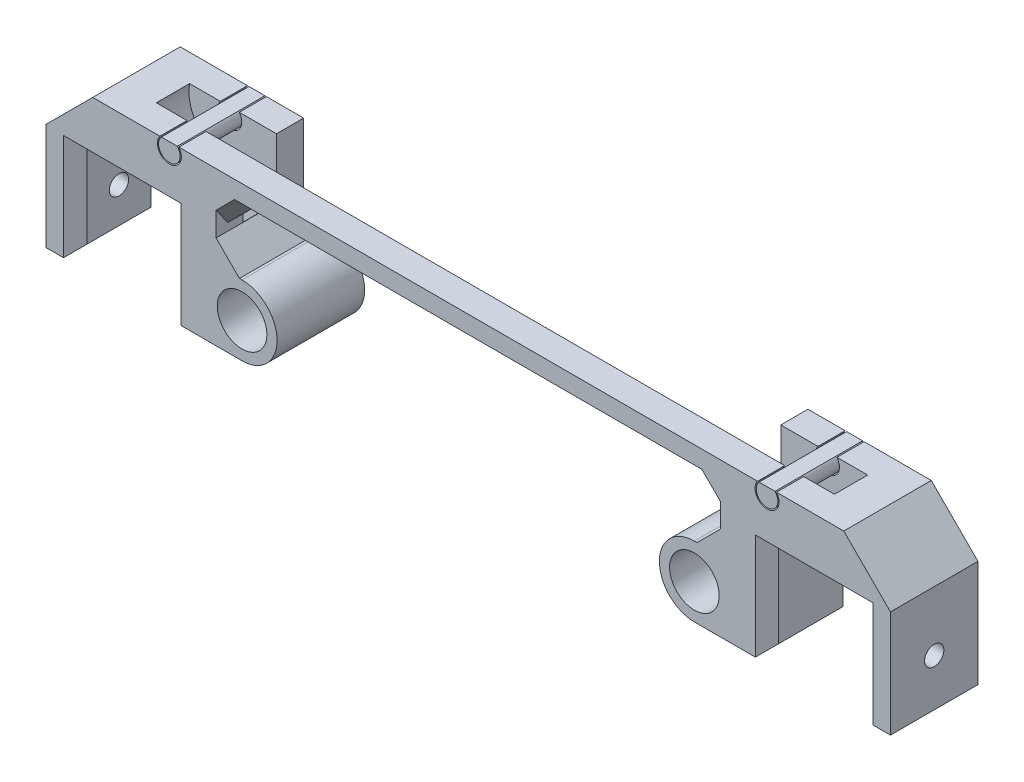
SolidWorks part; units mm, degrees
ref_plane "Front Plane" through (0, 0, 0) normal (0, 0, 1) x (1, 0, 0)
ref_plane "Top Plane" through (0, 0, 0) normal (0, 1, 0) x (1, 0, 0)
ref_plane "Right Plane" through (0, 0, 0) normal (1, 0, 0) x (0, 0, -1)
sketch "Sketch1" plane through (0, 0, 0) normal (0, 0, 1) x (1, 0, 0)
  line L0 (0, 0) -> (0, -36.7902) construction
  line L1 (-54.864, 0) -> (54.864, 0)
  line L2 (54.864, 0) -> (54.864, -27.0383)
  line L3 (54.864, -27.0383) -> (65.024, -27.0383)
  line L4 (65.024, -27.0383) -> (65.024, -6.5405)
  line L5 (65.024, -6.5405) -> (85.5218, -6.5405)
  line L6 (85.5218, -6.5405) -> (85.5218, -27.0383)
  line L7 (85.5218, -27.0383) -> (91.8718, -27.0383)
  line L8 (91.8718, -27.0383) -> (91.8718, 6.35)
  line L9 (91.8718, 6.35) -> (-91.8718, 6.35)
  line L10 (65.024, -6.5405) -> (65.024, -4.0005) construction
  line L11 (65.024, -4.0005) -> (65.024, 4.7625) construction
  line L12 (65.024, 4.7625) -> (65.024, 6.35) construction
  line L13 (65.024, 6.35) -> (65.024, 7.366) construction
  line L14 (-65.024, 6.35) -> (-65.024, 7.366) construction
  line L15 (-65.024, 4.7625) -> (-65.024, 6.35) construction
  line L16 (-65.024, -4.0005) -> (-65.024, 4.7625) construction
  line L17 (-65.024, -6.5405) -> (-65.024, -4.0005) construction
  line L18 (-91.8718, -27.0383) -> (-91.8718, 6.35)
  line L19 (-85.5218, -27.0383) -> (-91.8718, -27.0383)
  line L20 (-85.5218, -6.5405) -> (-85.5218, -27.0383)
  line L21 (-65.024, -6.5405) -> (-85.5218, -6.5405)
  line L22 (-65.024, -27.0383) -> (-65.024, -6.5405)
  line L23 (-54.864, -27.0383) -> (-65.024, -27.0383)
  line L24 (-54.864, 0) -> (-54.864, -27.0383)
  line L25 (65.024, -27.0383) -> (85.5218, -27.0383) construction
  circle A0 centre (65.024, 4.7625) radius 8.763 construction
  circle A1 centre (65.024, 4.7625) radius 2.6035
  circle A2 centre (-65.024, 4.7625) radius 8.763 construction
  circle A3 centre (-65.024, 4.7625) radius 2.6035
  point P26 (0, 6.35)
  dimension "D2" = 5.207
  dimension "D4" = 17.526
  dimension "D1" = 109.728
  dimension "D3" = 1.016
  dimension "D5" = 2.54
  dimension "D6" = 10.16
  dimension "D7" = 20.4978
  dimension "D8" = 6.35
  dimension "D9" = 6.35
  dimension "D10" = 130.048
  dimension "D11" = 171.0436
extrude "Boss-Extrude1" add sketch "Sketch1" along normal blind 19.05 contours L9 A3 L18 L19 L20 L21 L22 L23 L24 L1 L2 L3 L4 L5 L6 L7 L8 A1
hole_wizard "M5x0.8 Tapped Hole1" positions "Sketch9" profile "Sketch10" tap size "M5x0.8" standard "ANSI Metric" end condition up to next
sketch "Sketch9" plane through (91.8718, 0, 0) normal (1, 0, 0) x (0, 0, -1)
  line L0 (-9.525, -6.5405) -> (-9.525, -27.0383) construction
  line L1 (-19.05, -6.5405) -> (0, -6.5405) construction
  line L2 (-19.05, -27.0383) -> (0, -27.0383) construction
  point P0 (-9.525, -16.7894)
sketch "Sketch10" plane through (91.8718, -16.7894, 9.525) normal (0, 1, 0) x (0, 0, -1)
  line L0 (0, 0) -> (0, 6.35)
  line L1 (0, 6.35) -> (2.1, 6.35)
  line L2 (2.1, 6.35) -> (2.1, 0)
  line L5 (2.1, 0) -> (0, 0)
  line L11 (0, -6.35) -> (0, 107.95) construction
  dimension "Thru Tap Drill Dia." = 4.2
  dimension "Thru Tap Drill Depth" = 6.35
cosmetic thread "Hole Thread1" parameters "D2"=5
ref_plane "Plane1" through (0, 0, 9.525) normal (0, 0, 1) x (1, 0, 0)
sketch "Sketch2" plane through (0, 0, 9.525) normal (0, 0, 1) x (1, 0, 0)
  line L0 (65.024, -4.1275) -> (56.134, -4.1275)
  line L1 (56.134, -4.1275) -> (56.134, 4.7625)
  line L2 (56.134, 4.7625) -> (56.134, 13.6525)
  line L3 (56.134, 13.6525) -> (65.024, 13.6525)
  line L4 (56.134, -4.1275) -> (0, -4.1275)
  line L5 (0, -4.1275) -> (0, 13.6525)
  line L6 (0, 13.6525) -> (56.134, 13.6525)
  circle A0 centre (65.024, 4.7625) radius 8.89
  dimension "D1" = 17.78
extrude "Cut-Extrude1" cut sketch "Sketch2" against normal mid plane 7.239 contours L6 L5 L4 L1 L2 | A0 L3 L2 | A0 | A0 L1 L0
sketch "Sketch3" plane through (0, 0, 19.05) normal (0, 0, 1) x (1, 0, 0)
  line L0 (62.9605, 6.35) -> (67.0875, 6.35)
  line L1 (0, 0) -> (0, 34.2985) construction
  line L2 (-54.864, 0) -> (54.864, 0) construction
  line L3 (-62.9605, 6.35) -> (-67.0875, 6.35)
  circle A0 centre (65.024, 4.7625) radius 2.3495
  circle A1 centre (-65.024, 4.7625) radius 2.3495
  dimension "D1" = 4.699
extrude "Boss-Extrude2" add sketch "Sketch3" against normal blind 19.05 separate body contours L0 A0 | A1 L3
chamfer "Chamfer1" distance 2.54 angle 45 2 edges at (85.5218, -27.0383, 9.525) (65.024, -27.0383, 9.525)
chamfer "Chamfer2" distance 10.16 angle 45 1 edges at (91.8718, 6.35, 9.525)
mirror "Mirror1" about plane through (0, 0, 0) normal (1, 0, 0) of "M5x0.8 Tapped Hole1", "Chamfer2", "Chamfer1", "Boss-Extrude2", "Cut-Extrude1"
sketch "Sketch4" plane through (0, 6.35, 0) normal (0, 1, 0) x (1, 0, 0)
  line L0 (-54.864, -13.1445) -> (-54.864, 0)
  line L1 (-54.864, 0) -> (54.864, 0)
  line L2 (54.864, 0) -> (54.864, -13.1445)
  line L3 (54.864, -13.1445) -> (-54.864, -13.1445)
extrude "Cut-Extrude2" cut sketch "Sketch4" against normal through all
chamfer "Chamfer3" distance 2.54 angle 45 2 edges at (-54.864, -4.1275, 9.525) (54.864, -4.1275, 9.525)
chamfer "Chamfer6" distance 5.08 angle 45 2 edges at (54.864, 0, 16.0972) (-54.864, 0, 16.0972)
sketch "Sketch5" plane through (0, 0, 19.05) normal (0, 0, 1) x (1, 0, 0)
  line L0 (-54.864, -27.0383) -> (-49.2125, -27.0383)
  line L1 (-49.2125, -11.7983) -> (-54.864, -11.7983)
  line L2 (-54.864, -5.08) -> (-54.864, -27.0383) construction
  line L3 (-54.864, -11.7983) -> (-54.864, -27.0383)
  line L4 (-54.864, -19.4183) -> (-54.61, -19.4183) construction
  arc A0 (-49.2125, -27.0383) -> (-49.2125, -11.7983) centre (-49.2125, -19.4183) ccw
  circle A1 centre (-49.2125, -19.4183) radius 5.3975
  dimension "D1" = 10.795
  dimension "D2" = 7.62
  dimension "D3" = 0.254
extrude "Boss-Extrude3" add sketch "Sketch5" against normal up to surface (19.05 mm away) up to face at (-73.6053, -11.7563, 0)
ref_plane "Plane2" through (0, -14.0208, 0) normal (0, -1, 0) x (1, 0, 0)
sketch "Sketch6" plane through (0, -14.0208, 0) normal (0, -1, 0) x (1, 0, 0)
  line L0 (-49.2125, 0) -> (-49.2125, 19.05) construction
  circle A0 centre (-49.2125, 3.5712) radius 1.905
  dimension "D1" = 3.81
extrude "Boss-Extrude4" add sketch "Sketch6" along normal blind 1.778 draft 22.5
mirror "Mirror5" about plane through (0, 0, 0) normal (1, 0, 0) of "Boss-Extrude3", "Boss-Extrude4"
chamfer "Chamfer7" distance 5.08 angle 45 2 edges at (-54.864, -11.7983, 9.525) (54.864, -11.7983, 9.525)
chamfer "Chamfer4" distance 2.54 angle 45 4 edges at (0, 0, 19.05) (0, 0, 13.1445) (-52.324, -2.54, 19.05) (52.324, -2.54, 19.05)
chamfer "Chamfer5" distance 2.54 angle 45 12 edges at (-85.5218, -15.5194, 0) (-75.2729, -6.5405, 0) (-65.024, -15.5194, 0) (-65.024, -15.5194, 19.05) (-75.2729, -6.5405, 19.05) (-85.5218, -15.5194, 19.05) (85.5218, -15.5194, 0) (85.5218, -15.5194, 19.05) (75.2729, -6.5405, 0) (75.2729, -6.5405, 19.05) (65.024, -15.5194, 19.05) (65.024, -15.5194, 0)
sketch "Sketch7" plane through (0, 0, 13.1445) normal (0, 0, -1) x (-1, 0, 0)
  line L1 (-54.864, -6.7183) -> (54.864, -6.7183)
  line L2 (-54.864, -6.7183) -> (-54.864, 6.35)
  line L3 (-54.864, 6.35) -> (54.864, 6.35)
  line L4 (54.864, -6.7183) -> (54.864, 6.35)
extrude "Cut-Extrude3" [suppressed] cut sketch "Sketch7" against normal through all
